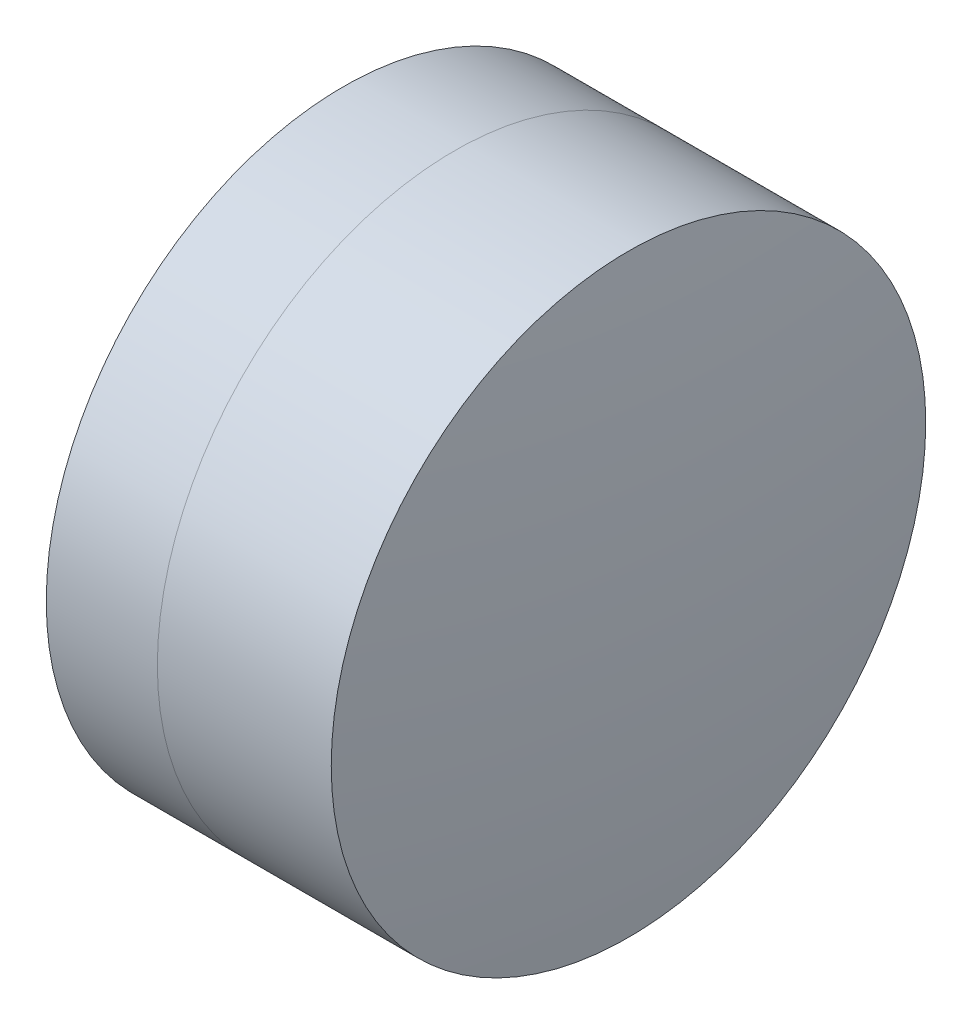
SolidWorks part; units mm, degrees
ref_plane "前视基准面" through (0, 0, 0) normal (0, 0, 1) x (1, 0, 0)
ref_plane "上视基准面" through (0, 0, 0) normal (0, 1, 0) x (1, 0, 0)
ref_plane "右视基准面" through (0, 0, 0) normal (1, 0, 0) x (0, 0, -1)
sketch "草图1" plane through (0, 0, 0) normal (0, 1, 0) x (1, 0, 0)
  line L0 (-9.7026, 0) -> (11.7646, 0) construction
  line L1 (-2.1941, -5) -> (-0.3254, -5)
  line L2 (-2.1941, 5) -> (-0.3254, 5)
  arc A0 (-0.3254, -5) -> (-0.3254, 5) centre (-6.6394, 0) ccw
  arc A1 (-2.1941, 5) -> (-2.1941, -5) centre (7.7026, 0) ccw
  point P10 (-3.3854, 0)
  point P11 (1.4146, 0)
  dimension "D3" = 11.088
  dimension "D4" = 8.054
  dimension "D1" = 5
  dimension "D2" = 5
  dimension "D5" = 4.8
revolve "旋转1" add sketch "草图1" angle 360 about L0
sketch "草图2" plane through (0, 0, 0) normal (0, 1, 0) x (1, 0, 0)
  line L0 (-0.5519, 0) -> (13.3053, 0) construction
  line L2 (-0.3254, 5) -> (2.5993, 5)
  line L3 (-0.3254, -5) -> (2.5993, -5)
  arc A0 (2.5993, -5) -> (2.5993, 5) centre (-36.8954, 0) ccw
  arc A1 (-0.3254, -5) -> (-0.3254, 5) centre (-6.6394, 0) ccw construction
  arc A2 (-0.3254, -5) -> (-0.3254, 5) centre (-6.6394, 0) ccw
  point P4 (1.4146, 0)
  point P8 (2.9146, 0)
  dimension "D1" = 39.81
  dimension "D2" = 1.5
revolve "旋转3" add sketch "草图2" angle 360 about L0
